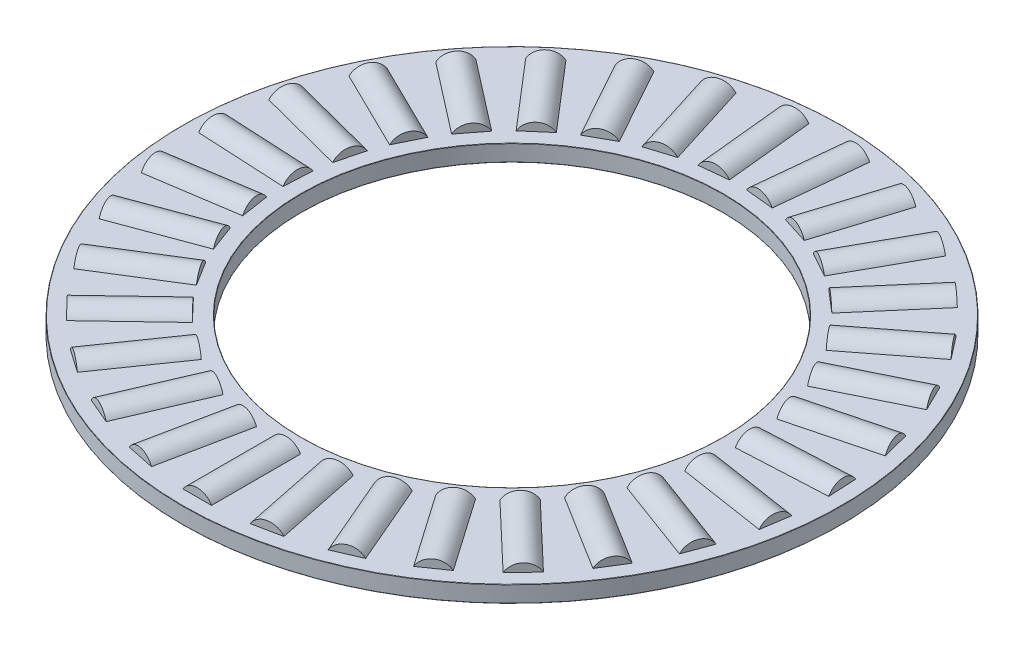
SolidWorks part; units mm, degrees
ref_plane "Front Plane" through (0, 0, 0) normal (0, 0, 1) x (1, 0, 0)
ref_plane "Top Plane" through (0, 0, 0) normal (0, 1, 0) x (1, 0, 0)
ref_plane "Right Plane" through (0, 0, 0) normal (1, 0, 0) x (0, 0, -1)
sketch "Sketch1" plane through (0, 0, 0) normal (1, 0, 0) x (0, 0, -1)
  line L0 (-19.8438, 0) -> (19.8438, 0) construction
  line L1 (0, -0.9922) -> (0, 0.9922) construction
  line L2 (-19.8438, 0.4961) -> (-12.7, 0.4961)
  line L3 (-19.8438, 0.4961) -> (-19.8438, -0.4961)
  line L4 (-19.8438, -0.4961) -> (-12.7, -0.4961)
  line L5 (-12.7, 0.4961) -> (-12.7, -0.4961)
  line L7 (-16.2719, 0.9922) -> (-16.2719, 0.4961) construction
  line L8 (-18.9508, 0.9922) -> (-13.593, 0.9922) construction
  line L9 (-18.9508, 0.9922) -> (-18.9508, -0.9922) construction
  line L10 (-18.9508, -0.9922) -> (-13.593, -0.9922) construction
  line L11 (-13.593, 0.9922) -> (-13.593, -0.9922) construction
  point P16 (-18.9508, 0)
  dimension "D1" = 5.3578
  dimension "OD" = 39.6875
  dimension "Shaft Dia" = 25.4
  dimension "Th" = 1.9844
  dimension "D2" = 0.9922
  dimension "D3" = 7.1438
revolve "Revolve1" add sketch "Sketch1" angle 360 about L1
sketch "Sketch3" plane through (0, 0, 0) normal (1, 0, 0) x (0, 0, -1)
  line L0 (-18.9508, 0.9922) -> (-18.9508, -0.9922) construction
  line L1 (-18.9508, 0) -> (-13.593, 0)
  line L2 (-18.9508, 0) -> (-18.9508, 0.9922)
  line L3 (-18.9508, 0.9922) -> (-13.593, 0.9922)
  line L4 (-13.593, 0) -> (-13.593, 0.9922)
revolve "Cut-Revolve1" cut sketch "Sketch3" angle 360 about L1
sketch "Sketch2" plane through (0, 0, 0) normal (1, 0, 0) x (0, 0, -1)
  line L1 (-18.9508, 0) -> (-13.593, 0)
  line L2 (-18.9508, 0) -> (-18.9508, 0.9922)
  line L3 (-18.9508, 0.9922) -> (-13.593, 0.9922)
  line L4 (-13.593, 0) -> (-13.593, 0.9922)
revolve "Revolve2" add sketch "Sketch2" angle 360 about L1
ref_axis "Axis1" through (0, 0.9922, 0) along (0, -1, 0)
pattern_circular "CirPattern1" count 31 every 11.613 about axis through (0, 0.9922, 0) along (0, -1, 0) of bodies 187 411
pattern_circular "CirPattern2" count 31 every 11.613 about axis through (0, 0, 0) along (0, 1, 0) of "Cut-Revolve1"
sketch "Sketch4" plane through (0, 0, 0) normal (1, 0, 0) x (0, 0, -1)
  line L0 (-19.8438, 0.4961) -> (-19.8438, -0.4961) construction
  line L1 (-19.8438, 9.1091) -> (-12.7, 9.1091)
  line L2 (-19.8438, 9.1091) -> (-19.8438, 9.9219)
  line L3 (-19.8438, 9.9219) -> (-12.7, 9.9219)
  line L4 (-12.7, 9.1091) -> (-12.7, 9.9219)
  line L5 (-19.8438, -9.9219) -> (-12.7, -9.9219)
  line L6 (-19.8438, -9.9219) -> (-19.8438, -9.1091)
  line L7 (-19.8438, -9.1091) -> (-12.7, -9.1091)
  line L8 (-12.7, -9.9219) -> (-12.7, -9.1091)
  line L10 (-12.7, 0.4961) -> (-12.7, -0.4961) construction
  line L11 (0, 0) -> (-19.8438, 0) construction
  line L12 (-19.8438, 0) -> (19.8438, 0) construction
  line L13 (0, -0.9922) -> (0, 0.9922) construction
  dimension "Ht" = 19.8438
  dimension "Washer Th" = 0.8128
  dimension "Washer ID" = 25.4
  dimension "Washer OD" = 39.6875
revolve "Revolve3" [suppressed] add sketch "Sketch4" angle 360 about L1
fillet "Fillet1" [suppressed] radius 0.0198
fillet "Fillet2" radius 0.0198 4 edges at (0, -0.4961, -12.7) (0, 0.4961, -12.7) (0, -0.4961, -19.8438) (0, 0.4961, -19.8438)
fillet "Fillet3" [suppressed] radius 0.0198
equation "\"D2@Sketch1\" = \"Th@Sketch1\"*.5"
equation "\"D1@Fillet1\" = \"Th@Sketch1\"*.01"
equation "\"D1@Fillet2\" = \"D1@Fillet1\""
equation "\"D1@Fillet3\" = \"D1@Fillet1\""
equation "\"D1@Sketch1\" = \"D3@Sketch1\"*.75"
equation "\"Angle@CirPattern1\" = 360/\"Rollers@CirPattern1\""
equation "\"Rollers@CirPattern1\" = \"OD@Sketch1\"*20"
equation "\"D1@CirPattern2\" = \"Rollers@CirPattern1\""
equation "\"D2@CirPattern2\" = \"Angle@CirPattern1\""
equation "\"Ht@Sketch4\" = \"Th@Sketch1\"*10"
